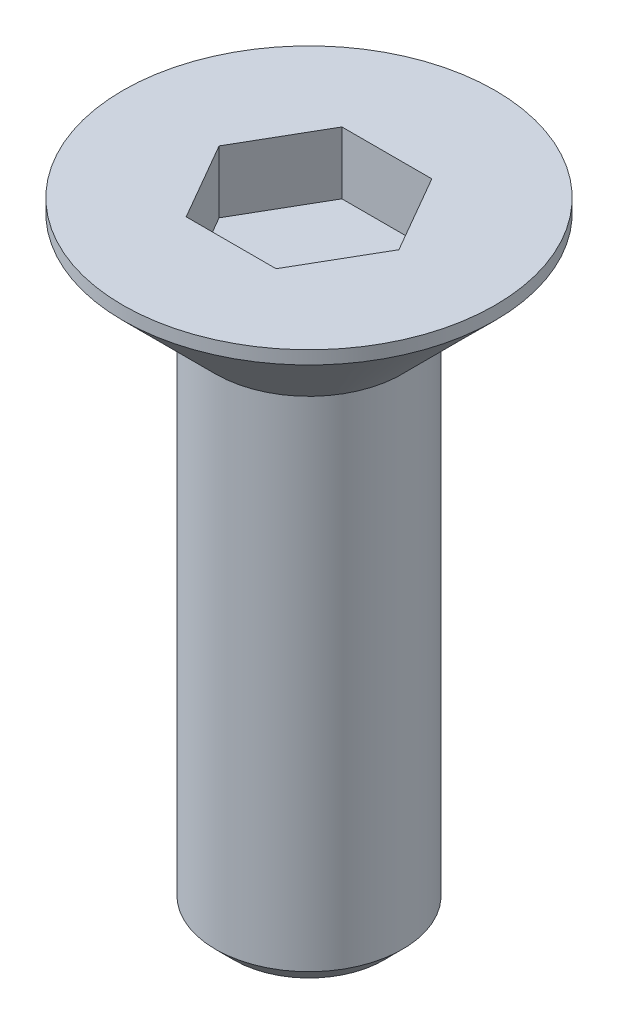
SolidWorks part; units mm, degrees
material "acero"
ref_plane "Alzado" through (0, 0, 0) normal (0, 0, 1) x (1, 0, 0)
ref_plane "Planta" through (0, 0, 0) normal (0, 1, 0) x (1, 0, 0)
ref_plane "Vista lateral" through (0, 0, 0) normal (1, 0, 0) x (0, 0, -1)
sketch "Croquis1" plane through (0, 0, 0) normal (0, 0, 1) x (1, 0, 0)
  line L0 (0, 0) -> (0, -60.9498) construction
  line L1 (0, 0) -> (3.2, 0)
  line L2 (1.5, -1.7) -> (3.2, 0)
  line L4 (1.5, -1.7) -> (1.5, -10)
  line L5 (1.5, -10) -> (0, -10)
  line L6 (0, -10) -> (0, 0)
  dimension "D1" = 10
  dimension "D2" = 45
  dimension "D3" = 1.7
  dimension "D4" = 3
revolve "Revolución1" add sketch "Croquis1" angle 360 about L0
chamfer "Chaflán2" distance 0.3 angle 45 1 edges at (0, 0, 3.2)
chamfer "Chaflán3" distance 0.3 angle 45 1 edges at (0, -10, 1.5)
sketch "Croquis3" plane through (0, 0, 0) normal (0, 1, 0) x (1, 0, 0)
  line L1 (-0.7217, 1.25) -> (-1.4434, 0)
  line L2 (-1.4434, 0) -> (-0.7217, -1.25)
  line L3 (-0.7217, -1.25) -> (0.7217, -1.25)
  line L4 (0.7217, -1.25) -> (1.4434, 0)
  line L5 (1.4434, 0) -> (0.7217, 1.25)
  line L6 (0.7217, 1.25) -> (-0.7217, 1.25)
  circle A0 centre (0, 0) radius 1.25 construction
  dimension "D1" = 2.5
extrude "Cortar-Extruir2" cut sketch "Croquis3" against normal blind 1
